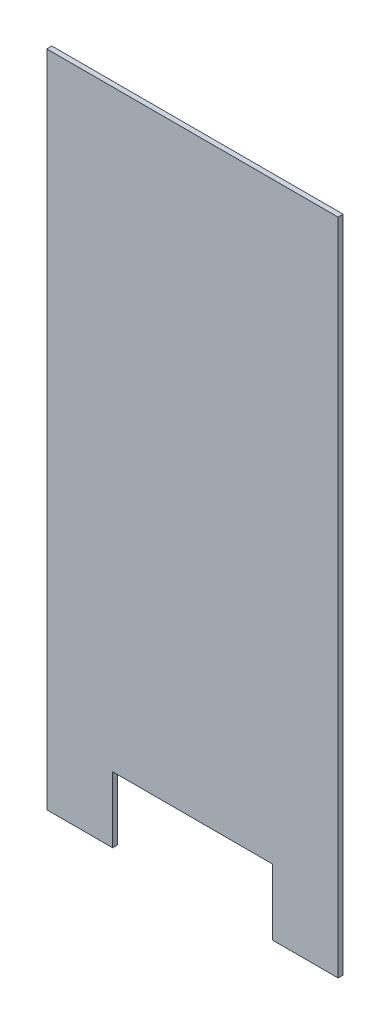
SolidWorks part; units mm, degrees
ref_plane "Front Plane" through (0, 0, 0) normal (0, 0, 1) x (1, 0, 0)
ref_plane "Top Plane" through (0, 0, 0) normal (0, 1, 0) x (1, 0, 0)
ref_plane "Right Plane" through (0, 0, 0) normal (1, 0, 0) x (0, 0, -1)
sketch "Sketch1" plane through (0, 0, 0) normal (0, 0, 1) x (1, 0, 0)
  line L0 (0, 0) -> (0, -650.25) construction
  line L1 (-287.5, 650.25) -> (287.5, 650.25)
  line L2 (-287.5, 650.25) -> (-287.5, -650.25)
  line L3 (-287.5, -650.25) -> (-157.5, -650.25)
  line L4 (287.5, 650.25) -> (287.5, -650.25)
  line L5 (-287.5, 650.25) -> (287.5, -650.25) construction
  line L6 (-287.5, -650.25) -> (287.5, 650.25) construction
  line L7 (157.5, -650.25) -> (287.5, -650.25)
  line L8 (-157.5, -520.25) -> (157.5, -520.25)
  line L9 (-157.5, -520.25) -> (-157.5, -650.25)
  line L11 (157.5, -520.25) -> (157.5, -650.25)
  line L12 (-157.5, -520.25) -> (157.5, -650.25) construction
  line L13 (-157.5, -650.25) -> (157.5, -520.25) construction
  point P0 (0, 0)
  point P8 (0, -585.25)
  dimension "D1" = 575
  dimension "D2" = 1300.5
  dimension "D3" = 315
  dimension "D4" = 130
extrude "Boss-Extrude1" add sketch "Sketch1" along normal blind 10
